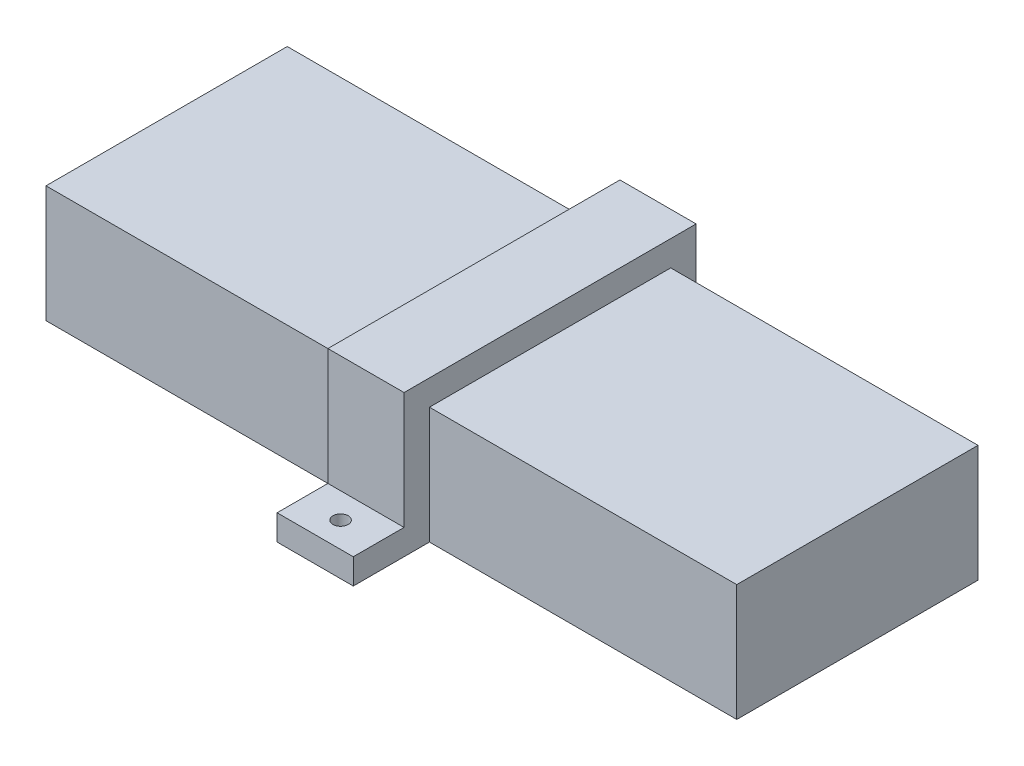
SolidWorks part; units mm, degrees
ref_plane "Front Plane" through (0, 0, 0) normal (0, 0, 1) x (1, 0, 0)
ref_plane "Top Plane" through (0, 0, 0) normal (0, 1, 0) x (1, 0, 0)
ref_plane "Right Plane" through (0, 0, 0) normal (1, 0, 0) x (0, 0, -1)
sketch "Sketch1" plane through (0, 0, 0) normal (0, 1, 0) x (1, 0, 0)
  line L1 (-68, -23.75) -> (68, -23.75)
  line L2 (-68, -23.75) -> (-68, 23.75)
  line L3 (-68, 23.75) -> (68, 23.75)
  line L4 (68, -23.75) -> (68, 23.75)
  line L5 (-68, -23.75) -> (68, 23.75) construction
  line L6 (-68, 23.75) -> (68, -23.75) construction
  point P0 (0, 0)
  dimension "D1" = 47.5
  dimension "D2" = 136
extrude "Boss-Extrude1" add sketch "Sketch1" along normal blind 23
sketch "Sketch5" plane through (0, 0, 0) normal (1, 0, 0) x (0, 0, -1)
  line L12 (41.8, 0) -> (-41.8, 0) construction
  line L13 (-23.75, 23) -> (-23.75, 0) construction
  line L25 (-23.75, 0) -> (23.75, 0)
  line L26 (-38.75, 5) -> (-38.75, 0)
  line L28 (-23.75, 23) -> (23.75, 23)
  line L30 (38.75, 0) -> (38.75, 5)
  line L31 (38.75, 5) -> (28.75, 5)
  line L32 (28.75, 5) -> (28.75, 28)
  line L33 (28.75, 28) -> (-28.75, 28)
  line L34 (-28.75, 28) -> (-28.75, 5)
  line L35 (-28.75, 5) -> (-38.75, 5)
  line L38 (-23.75, 23) -> (23.75, 23)
  line L39 (23.75, 0) -> (38.75, 0)
  line L40 (-38.75, 0) -> (-23.75, 0)
  line L41 (-23.75, 0) -> (-23.75, 23)
  line L42 (23.75, 23) -> (23.75, 0)
  dimension "D1" = 47.5
  dimension "D2" = 23
  dimension "D3" = 15
  dimension "D4" = 15
  dimension "D5" = 5
  dimension "D6" = 5
  dimension "D7" = 5
  dimension "D8" = 5
  dimension "D9" = 5
extrude "Boss-Extrude2" add sketch "Sketch5" along normal mid plane 15 separate body
sketch "Sketch6" plane through (0, 0, 0) normal (0, 1, 0) x (1, 0, 0)
  line L0 (0, -15.4) -> (0, 15.4) construction
  line L1 (7.5, -38.75) -> (-7.5, -38.75) construction
  line L2 (7.5, 38.75) -> (-7.5, 38.75) construction
  circle A0 centre (0, 33.75) radius 1.5
  circle A1 centre (0, -33.75) radius 1.5
  dimension "D1" = 3
  dimension "D2" = 5
  dimension "D3" = 5
extrude "Cut-Extrude1" cut sketch "Sketch6" along normal blind 10
